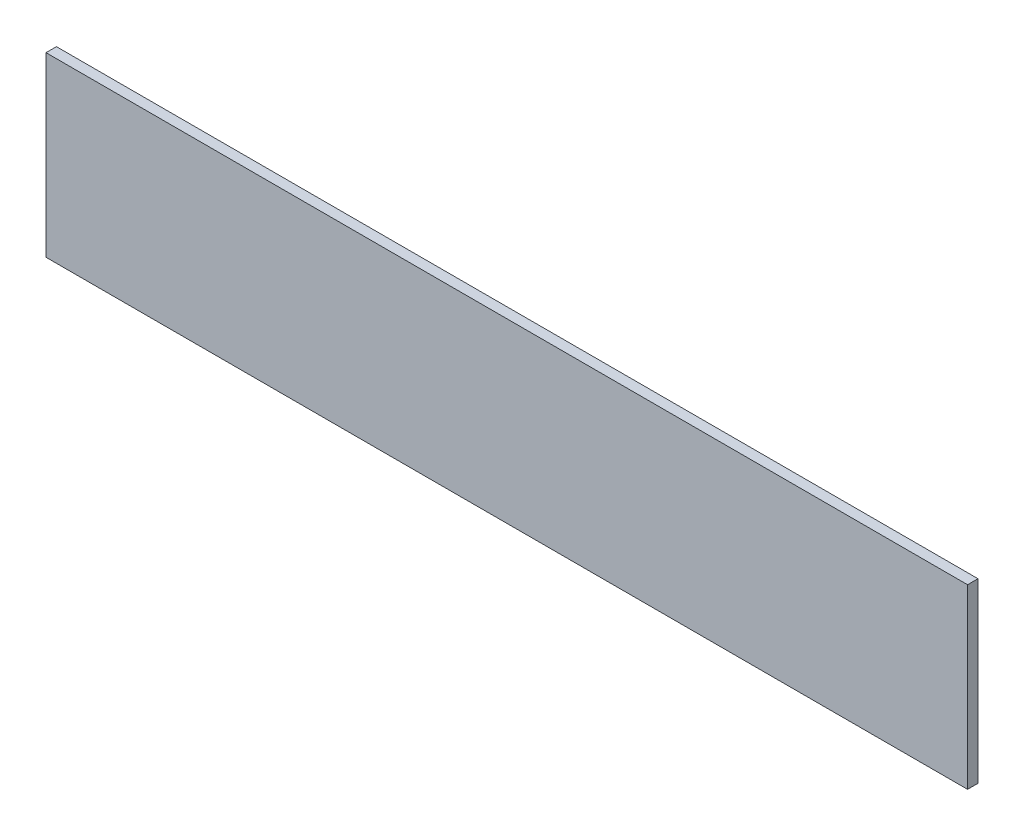
SolidWorks part; units mm, degrees
ref_plane "Front Plane" through (0, 0, 0) normal (0, 0, 1) x (1, 0, 0)
ref_plane "Top Plane" through (0, 0, 0) normal (0, 1, 0) x (1, 0, 0)
ref_plane "Right Plane" through (0, 0, 0) normal (1, 0, 0) x (0, 0, -1)
sketch "Sketch1" plane through (0, 0, 0) normal (0, 0, 1) x (1, 0, 0)
  line L1 (-42.1445, -2.6354) -> (46.2555, -2.6354)
  line L2 (-42.1445, -2.6354) -> (-42.1445, -19.6354)
  line L3 (-42.1445, -19.6354) -> (46.2555, -19.6354)
  line L4 (46.2555, -2.6354) -> (46.2555, -19.6354)
  dimension "D1" = 17
  dimension "D2" = 88.4
extrude "Boss-Extrude1" add sketch "Sketch1" along normal blind 1
